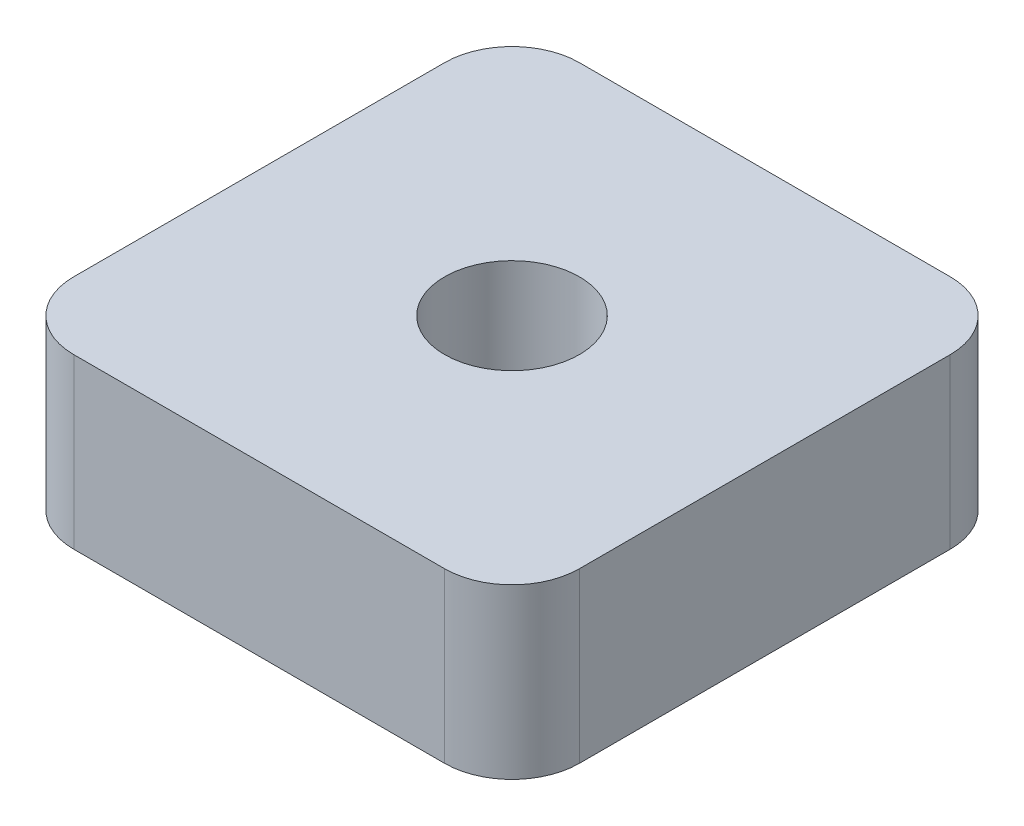
SolidWorks part; units mm, degrees
ref_plane "Front Plane" through (0, 0, 0) normal (0, 0, 1) x (1, 0, 0)
ref_plane "Top Plane" through (0, 0, 0) normal (0, 1, 0) x (1, 0, 0)
ref_plane "Right Plane" through (0, 0, 0) normal (1, 0, 0) x (0, 0, -1)
sketch "Sketch1" plane through (0, 0, 0) normal (0, 1, 0) x (1, 0, 0)
  line L1 (5.5, -7.5) -> (-5.5, -7.5)
  line L2 (7.5, -5.5) -> (7.5, 5.5)
  line L3 (5.5, 7.5) -> (-5.5, 7.5)
  line L4 (-7.5, -5.5) -> (-7.5, 5.5)
  line L5 (7.5, -7.5) -> (-7.5, 7.5) construction
  line L6 (7.5, 7.5) -> (-7.5, -7.5) construction
  circle A0 centre (0, 0) radius 2
  arc A1 (-7.5, -5.5) -> (-5.5, -7.5) centre (-5.5, -5.5) ccw
  arc A2 (7.5, -5.5) -> (5.5, -7.5) centre (5.5, -5.5) cw
  arc A3 (7.5, 5.5) -> (5.5, 7.5) centre (5.5, 5.5) ccw
  arc A4 (-5.5, 7.5) -> (-7.5, 5.5) centre (-5.5, 5.5) ccw
  point P0 (0, 0)
  dimension "D3" = 2
  dimension "D1" = 15
  dimension "D2" = 15
extrude "Boss-Extrude1" add sketch "Sketch1" along normal blind 5
